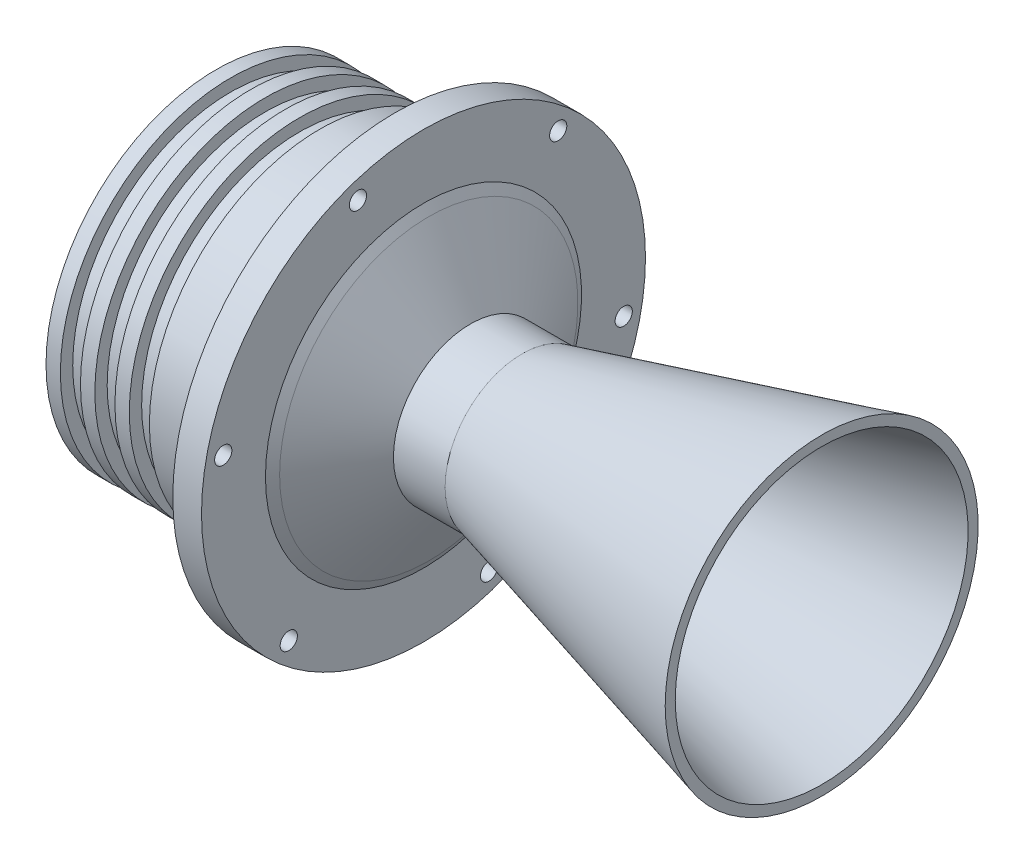
SolidWorks part; units mm, degrees
ref_plane "Plan de face" through (0, 0, 0) normal (0, 0, 1) x (1, 0, 0)
ref_plane "Plan de dessus" through (0, 0, 0) normal (0, 1, 0) x (1, 0, 0)
ref_plane "Plan de droite" through (0, 0, 0) normal (1, 0, 0) x (0, 0, -1)
sketch "Esquisse1" plane through (0, 0, 0) normal (0, 0, 1) x (1, 0, 0)
  line L0 (-113.6038, 0) -> (138.2965, 0) construction
  line L1 (75.139, 0) -> (75.139, 42.735) construction
  line L2 (-19.0393, 0) -> (-19.0393, 17.5) construction
  line L3 (-18.0393, 17.7679) -> (75.139, 42.735)
  line L7 (-19.0393, 17.5) -> (18.0829, 17.5) construction
  line L8 (18.0829, 17.5) -> (-75.9502, 17.5) construction
  line L9 (-19.2832, 17.8774) -> (-36.9712, 48.5139)
  line L10 (-19.9507, 33.0335) -> (-30.8642, 51.9362)
  line L13 (-19.9507, 33.0335) -> (-26.0129, 29.5335) construction
  line L14 (-68.851, 59.3) -> (-42.6997, 59.3)
  line L16 (-99.851, 50) -> (-49.7627, 50)
  line L17 (-76.4451, 55) -> (-76.4451, -5.7693) construction
  line L19 (-49.7627, 50) -> (-39.8526, 50)
  line L20 (-83.7986, 55) -> (-32.6997, 55) construction
  line L21 (-104.851, 59.3) -> (-99.851, 59.3)
  line L22 (-99.851, 59.3) -> (-99.851, 55)
  line L23 (-92.851, 55) -> (-92.851, 59.3)
  line L24 (-92.851, 59.3) -> (-87.851, 59.3)
  line L25 (75.139, 42.735) -> (105.9607, 50.9936)
  line L26 (-87.851, 59.3) -> (-87.851, 55)
  line L27 (-87.851, 55) -> (-80.851, 55)
  line L28 (-80.851, 55) -> (-80.851, 59.3)
  line L29 (-80.851, 59.3) -> (-75.851, 59.3)
  line L32 (-92.851, 55) -> (-99.851, 55)
  line L33 (-75.851, 59.3) -> (-75.851, 55)
  line L36 (-75.851, 55) -> (-68.851, 55)
  line L39 (105.9607, 50.9936) -> (105.9607, 54.4936)
  line L40 (-68.851, 55) -> (-68.851, 59.3)
  line L43 (-42.6997, 59.3) -> (-32.6997, 59.3) construction
  line L50 (-83.7986, 55) -> (-137.5237, 55) construction
  line L51 (48.1207, 39.1189) -> (49.0265, 35.7382) construction
  line L52 (-42.6997, 77.3) -> (-32.6997, 77.3)
  line L53 (-32.6997, 77.3) -> (-32.6997, 59.3)
  line L54 (-30.8642, 51.9362) -> (-32.6997, 55.0335) construction
  line L55 (-32.6997, 59.1351) -> (-32.6997, 55.0335) construction
  line L56 (-42.6997, 77.3) -> (-42.6997, 59.3)
  line L57 (-32.6997, 59.1351) -> (-32.6997, 59.3) construction
  line L58 (-104.851, 59.3) -> (-99.851, 50)
  line L61 (-19.9507, 33.0335) -> (-16.3597, 26.8138)
  line L62 (-16.3597, 26.8138) -> (1.6403, 26.8138)
  line L63 (-30.8642, 51.9362) -> (-32.6997, 55.0335)
  line L64 (-32.6997, 55.0335) -> (-32.6997, 58.336)
  line L65 (-32.6997, 59.3) -> (-32.6997, 58.336)
  line L66 (105.9607, 54.4936) -> (1.6403, 26.8138)
  arc A0 (-39.8526, 50) -> (-36.9712, 48.5139) centre (-40.1019, 45.9802) cw
  arc A1 (-18.0393, 17.7679) -> (-19.2832, 17.8774) centre (-18.5624, 18.9465) cw
  dimension "D1" = 42.735
  dimension "D2" = 17.5
  dimension "D4" = 59.3
  dimension "D5" = 15
  dimension "D6" = 15
  dimension "D7" = 94.1783
  dimension "D8" = 60
  dimension "D9" = 7
  dimension "D10" = 124
  dimension "D11" = 7
  dimension "D12" = 151.5841
  dimension "D13" = 94.1783
  dimension "D14" = 4.3
  dimension "D15" = 5
  dimension "D16" = 4.3
  dimension "D17" = 5
  dimension "D18" = 5
  dimension "D19" = 7
  dimension "D20" = 7
  dimension "D21" = 18
  dimension "D22" = 18
  dimension "D23" = 10
  dimension "D24" = 18
  dimension "D25" = 18
  dimension "D26" = 125
  dimension "D27" = 50.9936
  dimension "D28" = 55
  dimension "D30" = 3.5
  dimension "D33" = 3.5
  dimension "D34" = 77.3
  dimension "D37" = 22
revolve "Révolution1" add sketch "Esquisse1" angle 360 about L0
sketch "Esquisse2" plane through (0, 0, 0) normal (1, 0, 0) x (0, 0, -1)
  line L1 (-69.7269, 13.9057) -> (-46.9061, -53.4325)
  line L2 (-46.9061, -53.4325) -> (22.8208, -67.3381)
  line L3 (22.8208, -67.3381) -> (69.7269, -13.9057)
  line L4 (69.7269, -13.9057) -> (46.9061, 53.4325)
  line L5 (46.9061, 53.4325) -> (-22.8208, 67.3381)
  line L6 (-22.8208, 67.3381) -> (-69.7269, 13.9057)
  circle A0 centre (0, 0) radius 71.1
  circle A1 centre (0, 0) radius 77.3 construction
  circle A2 centre (0, 0) radius 61.5744 construction
  circle A3 centre (-69.7269, 13.9057) radius 3
  circle A4 centre (-46.9061, -53.4325) radius 3
  circle A5 centre (22.8208, -67.3381) radius 3
  circle A6 centre (69.7269, -13.9057) radius 3
  circle A7 centre (46.9061, 53.4325) radius 3
  circle A8 centre (-22.8208, 67.3381) radius 3
  circle A9 centre (0, 0) radius 59.3 construction
  dimension "D1" = 6.2
  dimension "D2" = 6
  dimension "D3" = 6
  dimension "D4" = 6
  dimension "D5" = 6
  dimension "D6" = 6
  dimension "D7" = 6
  dimension "D8" = 11.8
  dimension "D10" = 142.2
  dimension "D9" = 71.1
extrude "Enlèv. mat.-Extru.1" cut sketch "Esquisse2" against normal blind 448 and the other way blind 10 contours A3 | A4 | A5 | A6 | A7 | A8
